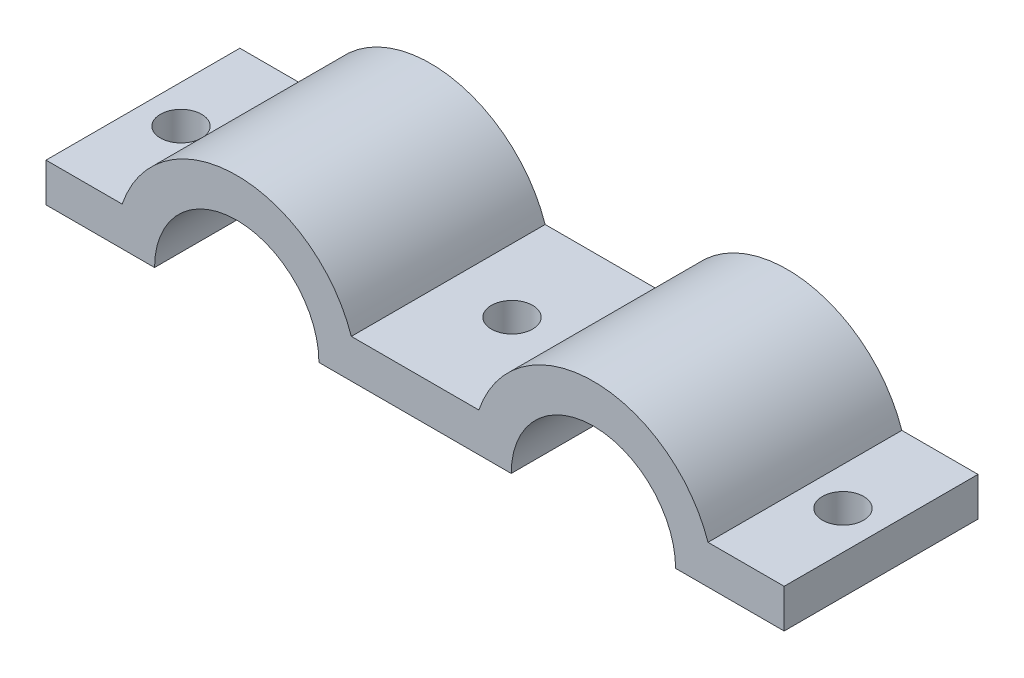
SolidWorks part; units mm, degrees
ref_plane "Front Plane" through (0, 0, 0) normal (0, 0, 1) x (1, 0, 0)
ref_plane "Top Plane" through (0, 0, 0) normal (0, 1, 0) x (1, 0, 0)
ref_plane "Right Plane" through (0, 0, 0) normal (1, 0, 0) x (0, 0, -1)
sketch "Sketch1" plane through (0, 0, 0) normal (0, 0, 1) x (1, 0, 0)
  line L21 (12.4752, 6.35) -> (0, 6.35)
  line L22 (0, 6.35) -> (0, 0)
  line L23 (0, 0) -> (17.78, 0)
  line L25 (50.0088, 6.35) -> (70.8952, 6.35)
  line L27 (76.2, 0) -> (44.704, 0)
  line L28 (60.452, 30.5681) -> (60.452, -25.4763) construction
  line L29 (120.904, 0) -> (103.124, 0)
  line L30 (120.904, 6.35) -> (120.904, 0)
  line L31 (108.4288, 6.35) -> (120.904, 6.35)
  arc A2 (17.78, 0) -> (44.704, 0) centre (31.242, 0) cw
  arc A4 (12.4752, 6.35) -> (50.0088, 6.35) centre (31.242, 0) cw
  arc A5 (108.4288, 6.35) -> (70.8952, 6.35) centre (89.662, 0) ccw
  arc A6 (103.124, 0) -> (76.2, 0) centre (89.662, 0) ccw
  point P6 (31.242, 13.462)
  point P12 (60.452, 6.35)
  point P20 (60.452, 0)
  dimension "D1" = 6.35
  dimension "D4" = 6.35
  dimension "D8" = 60.452
  dimension "D5" = 17.78
  dimension "D3" = 13.462
  dimension "D6" = 19.812
  dimension "D7" = 13.462
extrude "Boss-Extrude1" add sketch "Sketch1" along normal blind 31.75
sketch "Sketch3" plane through (0, 6.35, 0) normal (0, 1, 0) x (1, 0, 0)
  line L1 (60.452, 27.6941) -> (60.452, -48.8787) construction
  line L2 (0, -31.75) -> (0, 0) construction
  line L3 (12.4752, -31.75) -> (0, -31.75) construction
  circle A4 centre (6.2376, -15.875) radius 3.3782
  circle A5 centre (60.452, -15.875) radius 3.3782
  circle A6 centre (114.6664, -15.875) radius 3.3782
  point P12 (6.2376, -31.75)
  point P13 (0, -15.875)
  dimension "D1" = 6.7564
  dimension "D2" = 6.7564
  dimension "D3" = 60.452
extrude "Cut-Extrude1" cut sketch "Sketch3" against normal through all
